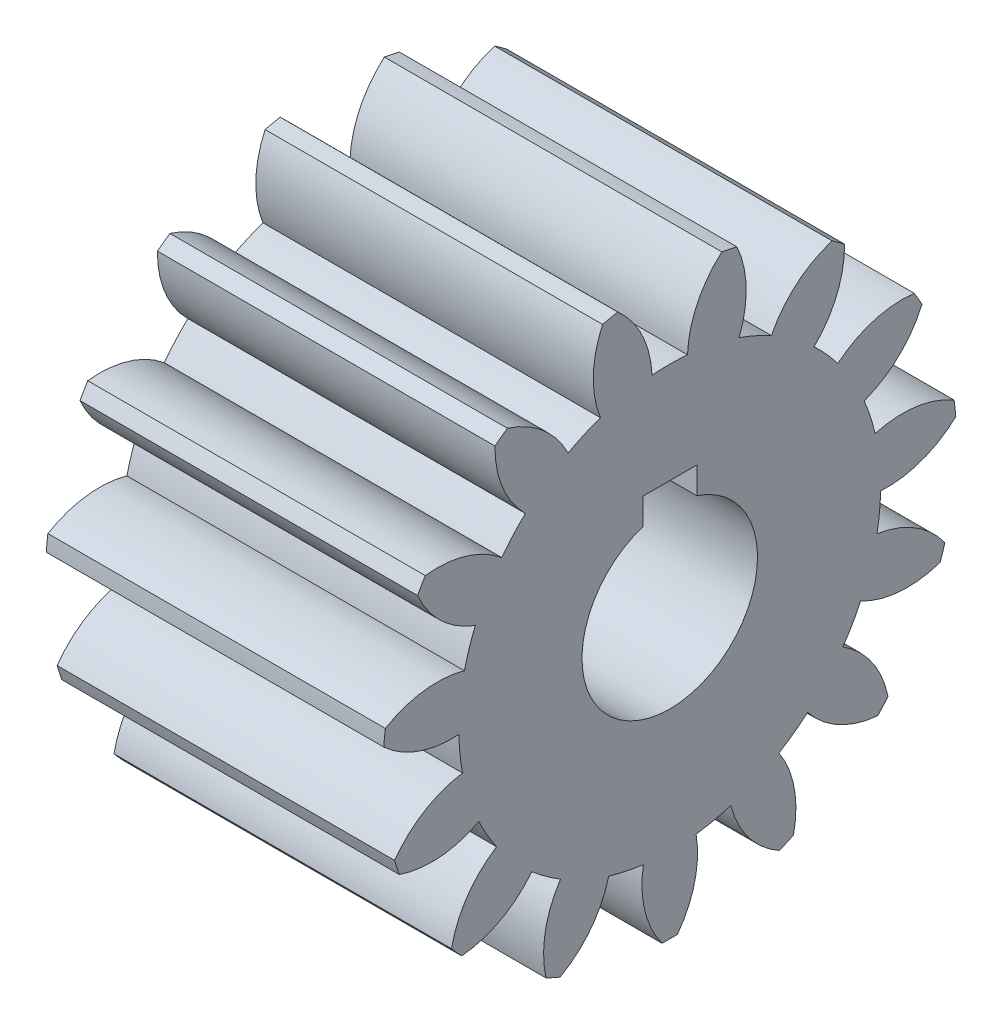
SolidWorks part; units mm, degrees
ref_plane "Plane1" through (0, 0, 0) normal (0, 0, 1) x (1, 0, 0)
ref_plane "Plane2" through (0, 0, 0) normal (0, 1, 0) x (1, 0, 0)
ref_plane "Plane3" through (0, 0, 0) normal (1, 0, 0) x (0, 0, -1)
sketch "HoldingSke" plane through (0, 0, 0) normal (0, 1, 0) x (1, 0, 0)
  line L0 (0, 0) -> (0.1932, -0.0518)
  line L1 (-15, 0) -> (100, 0) construction
  line L2 (0, 0) -> (-2.1039, 2.3779)
  line L3 (0, 0) -> (-11.863, 4.5341)
  line L4 (0, 0) -> (8.3417, 2.2352)
  line L5 (0, 0) -> (-46.8476, -17.4728)
  line L6 (0, 0) -> (-41.4481, -27.9652)
  line L7 (-2.1039, 2.3779) -> (8.6586, 51.2059)
  line L8 (-76.2, 54.61) -> (-72.9, 54.61)
  line L9 (-71.009, 38.7566) -> (-53.1078, 45.2721)
  line L10 (-76.2, 71.12) -> (104.1128, 71.12)
  line L11 (0, 0) -> (-50, 0)
  line L12 (-76.2, 101.6) -> (-76.033, 101.6)
  line L13 (24.9733, 27.94) -> (52.9518, 28.4284)
  line L14 (24.9733, 27.94) -> (24.9743, 27.94)
  line L15 (24.9733, 27.94) -> (100.4006, 29.5858)
  line L16 (-63.627, -5) -> (-12.827, -5)
  circle A0 centre (0, 0) radius 13
  circle A1 centre (0, 0) radius 31.249
  circle A2 centre (0, 0) radius 37.5
  circle A3 centre (0, 0) radius 13
  dimension "MHD" = 62.498
  dimension "Hub_dia" = 75
  dimension "Bore" = 26
  dimension "MBD" = 26
  dimension "Num_teeth" = 15
  dimension "Pitch" = 0.2
  dimension "Overall_len" = 50
  dimension "Show_teeth" = 15
  dimension "Thickness" = 50
  dimension "OAL" = 50.0001
  dimension "T_dim" = 3.3
  dimension "Ap" = 20
  dimension "H" = 19.05
  dimension "Pitch_radius" = 180.3128
  dimension "Width" = 50
  dimension "Backlash" = 0.167
  dimension "Addendum_fac" = 1
  dimension "Dedendum_fac" = 1.25
  dimension "Clearance_fac" = 0.25
  dimension "Dedendum_add" = 0.001
  dimension "Module" = 5
sketch "BasProSke" plane through (0, 0, 0) normal (0, 1, 0) x (1, 0, 0)
  line L0 (-10, 0) -> (60, 0) construction
  line L1 (0, 0) -> (0, 42.5)
  line L2 (0, 0) -> (50, 0)
  line L3 (50, 0) -> (50, 42.5)
  line L4 (50, 42.5) -> (0, 42.5)
  dimension "Thickness" = 50
  dimension "Diameter" = 85
revolve "Base-Revolve" add sketch "BasProSke" angle 360 about L0
sketch "TooCutSke" plane through (0, 0, 0) normal (1, 0, 0) x (0, 0, -1)
  line L1 (0, 0) -> (0, 107) construction
  line L2 (0, 0) -> (-4.2118, 37.2627) construction
  line L3 (0, 0) -> (-15.5202, 73.017) construction
  line L4 (-4.2118, 37.2627) -> (-7.7601, 36.5085) construction
  arc A0 (2.6245, 31.1386) -> (-2.6245, 31.1386) centre (0, 0) ccw
  arc A1 (7.7397, 41.8152) -> (-7.7397, 41.8152) centre (0, 0) ccw
  circle A2 centre (0, 0) radius 37.5 construction
  circle A3 centre (0, 0) radius 35.2385 construction
  arc A4 (-2.6245, 31.1386) -> (-7.7397, 41.8152) centre (-17.6118, 30.5217) ccw
  arc A5 (7.7397, 41.8152) -> (2.6245, 31.1386) centre (17.6118, 30.5217) ccw
  dimension "Root_dia" = 62.498
  dimension "Overcut_dia" = 85.0508
  dimension "Pitch_dia" = 75
  dimension "Base_dia" = 70.4769
  dimension "Flank_rad" = 15
  dimension "Half_ang" = 12
  dimension "Half_CT" = 3.6276
extrude "ToothCut" cut sketch "TooCutSke" along normal through all
fillet "Breaks" [suppressed] radius 0.1
fillet "RootFillets" [suppressed] radius 1.251
pattern_circular "TeethCuts" count 15 every 24 about axis through (-10, 0, 0) along (1, 0, 0) of "ToothCut", "RootFillets", "Breaks"
sketch "HubNeaOneSke" plane through (0, 0, 0) normal (-1, 0, 0) x (0, 0, 1)
  circle A0 centre (0, 0) radius 31.249
  dimension "Diameter" = 62.498
extrude "HubNearOne" [suppressed] add sketch "HubNeaOneSke" along normal blind 12.7001
sketch "HubNeaBotSke" plane through (0, 0, 0) normal (-1, 0, 0) x (0, 0, 1)
  circle A0 centre (0, 0) radius 31.249
  dimension "Diameter" = 62.498
extrude "HubNearBoth" [suppressed] add sketch "HubNeaBotSke" along normal blind 6.35
ref_plane "FarPln" through (50, 0, 0) normal (1, 0, 0) x (0, 0, -1)
sketch "HubFarSke" plane through (50, 0, 0) normal (1, 0, 0) x (0, 0, -1)
  circle A0 centre (0, 0) radius 31.249
  dimension "Diameter" = 62.498
extrude "HubFar" [suppressed] add sketch "HubFarSke" along normal blind 6.35
sketch "BorSke" plane through (0, 0, 0) normal (1, 0, 0) x (0, 0, -1)
  circle A0 centre (0, 0) radius 13
  dimension "Diameter" = 26
extrude "Bore" cut sketch "BorSke" along normal mid plane 100.0001
sketch "KeySke" plane through (0, 0, 0) normal (1, 0, 0) x (0, 0, -1)
  line L0 (-4, 0) -> (-4, 16.3)
  line L1 (-4, 16.3) -> (4, 16.3)
  line L2 (4, 16.3) -> (4, 0)
  line L3 (0, 0) -> (0, 34) construction
  line L4 (-4, 0) -> (4, 0)
  dimension "Offset" = 16.3
  dimension "Width" = 8
extrude "Keyway" cut sketch "KeySke" along normal mid plane 100.0001
pattern_circular "Keyway2" [suppressed] count 2 every 90 about axis through (-10, 0, 0) along (1, 0, 0)
equation "' \"Module@HoldingSke\" = 6.35"
equation "' \"Num_teeth@HoldingSke\" = 12"
equation "' \"Ap@HoldingSke\" =  20"
equation "' \"Ap@HoldingSke\" = 20"
equation "' \"Width@HoldingSke\" = 0.5 * 25.4"
equation "' \"Hub_dia@HoldingSke\"= 1 * 25.4"
equation "' \"Hub_dia@HoldingSke\" = 1 * 25.4"
equation "' \"Overall_len@HoldingSke\" = 1.0 * 25.4"
equation "' \"Bore@HoldingSke\" = 0.75 * 25.4"
equation "' \"T_dim@HoldingSke\" = 0.1 * 25.4"
equation "' \"Width@KeySke\" = 0.25 * 25.4"
equation "' \"Show_teeth@HoldingSke\" = 13"
equation "' \"Backlash@HoldingSke\" = 0.009 * 25.4"
equation "' \"Addendum_fac@HoldingSke\" = 1.0"
equation "' \"Dedendum_fac@HoldingSke\" = 1.25"
equation "' \"Dedendum_add@HoldingSke\" = 0.00005 * 25.4"
equation "' \"Clearance_fac@HoldingSke\" = 0.25"
equation "\"Pitch@HoldingSke\" = 1 / \"Module@HoldingSke\""
equation "\"Overcut_dia@TooCutSke\" = (\"Num_teeth@HoldingSke\" + 2 * \"Addendum_fac@HoldingSke\") / \"Pitch@HoldingSke\" + 0.002 * 25.4"
equation "\"Pitch_dia@TooCutSke\" = \"Num_teeth@HoldingSke\" / \"Pitch@HoldingSke\""
equation "\"Base_dia@TooCutSke\" = \"Num_teeth@HoldingSke\" / \"Pitch@HoldingSke\" * cos((\"Ap@HoldingSke\"  * 3.14159265 / 180))"
equation "\"Root_dia@TooCutSke\" = (\"Num_teeth@HoldingSke\" + 2) / \"Pitch@HoldingSke\" - 2 * (\"Addendum_fac@HoldingSke\" + \"Dedendum_fac@HoldingSke\") / \"Pitch@HoldingSke\" - \"Dedendum_add@HoldingSke\" * 2"
equation "\"Half_ang@TooCutSke\" = 180 / \"Num_teeth@HoldingSke\""
equation "\"Half_CT@TooCutSke\" = \"Num_teeth@HoldingSke\" / \"Pitch@HoldingSke\" * sin((3.14159265 / 2 / \"Num_teeth@HoldingSke\")) / 2 - 7 * \"Backlash@HoldingSke\" / 4"
equation "\"Flank_rad@TooCutSke\" = \"Num_teeth@HoldingSke\" / \"Pitch@HoldingSke\" / 5"
equation "\"Radius@RootFillets\" = \"Clearance_fac@HoldingSke\" / \"Pitch@HoldingSke\" + \"Dedendum_add@HoldingSke\""
equation "\"Break_rad@Breaks\" = 0.02 / \"Pitch@HoldingSke\""
equation "\"Thickness@HoldingSke\" = \"Width@HoldingSke\""
equation "\"OAL@HoldingSke\" = \"Thickness@HoldingSke\""
equation "\"MHD@HoldingSke\" = (\"Num_teeth@HoldingSke\" + 2) / \"Pitch@HoldingSke\" - 2 * (\"Addendum_fac@HoldingSke\" + \"Dedendum_fac@HoldingSke\")  / \"Pitch@HoldingSke\" - \"Dedendum_add@HoldingSke\" * 2"
equation "\"MBD@HoldingSke\" = (\"Num_teeth@HoldingSke\" + 2) / \"Pitch@HoldingSke\" - 2 * (\"Addendum_fac@HoldingSke\" + \"Dedendum_fac@HoldingSke\")  / \"Pitch@HoldingSke\" - \"Dedendum_add@HoldingSke\" * 2 - 0.002 * 25.4"
equation "\"MHD@HoldingSke\" = ((sgn( \"MHD@HoldingSke\" - \"Hub_dia@HoldingSke\" )-1)*( \"MHD@HoldingSke\" - \"Hub_dia@HoldingSke\" ))/-2+ \"Hub_dia@HoldingSke\""
equation "\"MBD@HoldingSke\" = ((sgn( \"MBD@HoldingSke\" - \"Bore@HoldingSke\" )-1)*( \"MBD@HoldingSke\" - \"Bore@HoldingSke\" ))/-2+ \"Bore@HoldingSke\""
equation "\"OAL@HoldingSke\" = ((sgn( \"OAL@HoldingSke\" - \"Overall_len@HoldingSke\" )+1)*( \"OAL@HoldingSke\" - \"Overall_len@HoldingSke\" ))/2 + \"Overall_len@HoldingSke\" + 0.000002 * 25.4"
equation "\"Num_teeth@TeethCuts\" = int( \"Show_teeth@HoldingSke\" ) + 1"
equation "\"Num_teeth@TeethCuts\" = ((sgn( \"Num_teeth@TeethCuts\" - \"Num_teeth@HoldingSke\" )-1)*( \"Num_teeth@TeethCuts\" - \"Num_teeth@HoldingSke\" ))/-2+ \"Num_teeth@HoldingSke\""
equation "\"Num_teeth@TeethCuts\" = ((sgn( \"Num_teeth@TeethCuts\" - 2.0)+1)*( \"Num_teeth@TeethCuts\" - 2.0))/2 +2.0"
equation "\"Angle@TeethCuts\" = 360.0 / \"Num_teeth@HoldingSke\""
equation "\"Diameter@BasProSke\" = (\"Num_teeth@HoldingSke\" + 2 * \"Addendum_fac@HoldingSke\") / \"Pitch@HoldingSke\""
equation "\"Thickness@BasProSke\"  = \"Thickness@HoldingSke\""
equation "' \"Fillet_rad@BasProSke\" =  \"Thickness@HoldingSke\" * 0.05"
equation "' \"Fillet_rad@BasProSke\" = \"Thickness@HoldingSke\" * 0.05"
equation "\"MHD@HoldingSke\" = ((sgn( \"MHD@HoldingSke\" - \"Root_dia@TooCutSke\" )-1)*( \"MHD@HoldingSke\" - \"Root_dia@TooCutSke\" ))/-2+ \"Root_dia@TooCutSke\""
equation "\"Diameter@HubNeaOneSke\" = \"MHD@HoldingSke\""
equation "\"Length@HubNearOne\" = \"OAL@HoldingSke\" - \"Thickness@BasProSke\""
equation "\"Diameter@HubNeaBotSke\" = \"MHD@HoldingSke\""
equation "\"Length@HubNearBoth\" = ( \"OAL@HoldingSke\" - \"Thickness@BasProSke\" ) / 2.0"
equation "\"Thickness@FarPln\" = \"Thickness@BasProSke\""
equation "\"Diameter@HubFarSke\" = \"MHD@HoldingSke\""
equation "\"Length@HubFar\" = ( \"OAL@HoldingSke\" - \"Thickness@BasProSke\" ) / 2.0"
equation "\"Diameter@BorSke\" = \"MBD@HoldingSke\""
equation "\"D1@Bore\" = \"OAL@HoldingSke\" * 2.0"
equation "\"D1@Keyway\" = \"OAL@HoldingSke\" * 2.0"
equation "\"Offset@KeySke\" = \"T_dim@HoldingSke\" + \"MBD@HoldingSke\" / 2.0"
